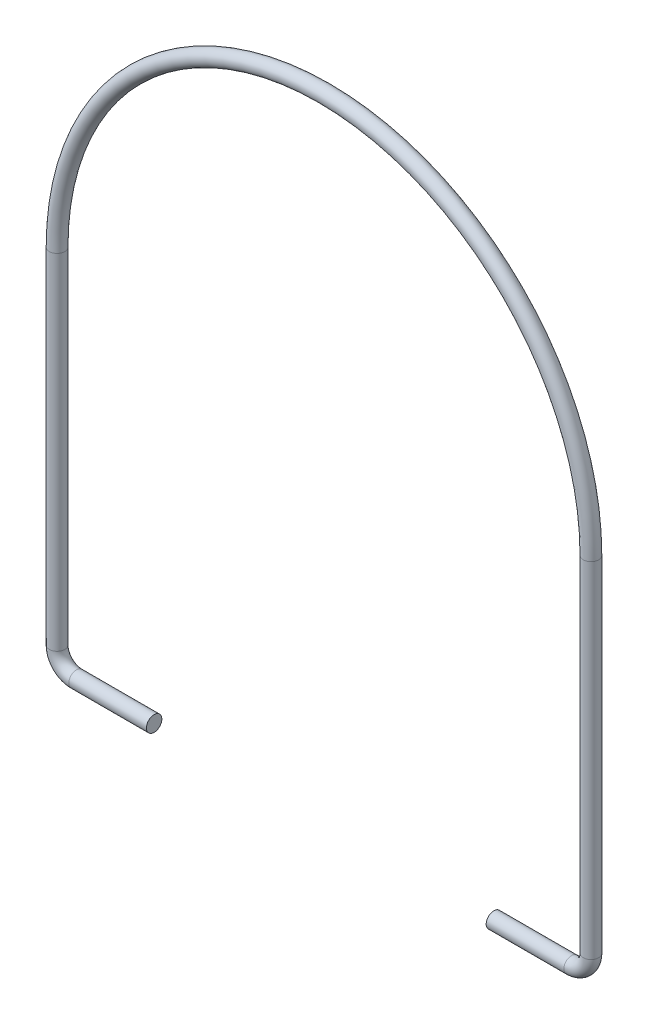
SolidWorks part; units mm, degrees
ref_plane "Front Plane" through (0, 0, 0) normal (0, 0, 1) x (1, 0, 0)
ref_plane "Top Plane" through (0, 0, 0) normal (0, 1, 0) x (1, 0, 0)
ref_plane "Right Plane" through (0, 0, 0) normal (1, 0, 0) x (0, 0, -1)
sketch "Sketch1" plane through (0, 0, 0) normal (0, 0, 1) x (1, 0, 0)
  line L0 (0, 0) -> (-16, 0)
  line L1 (-20, 4) -> (-20, 75)
  line L3 (90, 75) -> (90, 4)
  line L4 (86, 0) -> (70, 0)
  arc A0 (90, 75) -> (-20, 75) centre (35, 75) ccw
  arc A1 (90, 4) -> (86, 0) centre (86, 4) cw
  arc A2 (-20, 4) -> (-16, 0) centre (-16, 4) ccw
  point P10 (90, 0)
  point P13 (-20, 0)
  dimension "D1" = 75
  dimension "D4" = 55
  dimension "D5" = 4
  dimension "D2" = 20
  dimension "D3" = 20
sketch "Sketch2" plane through (0, 0, 0) normal (1, 0, 0) x (0, 0, -1)
  circle A0 centre (0, 0) radius 1.5875
  dimension "D1" = 3.175
sweep "Sweep1" add profiles "Sketch2" path "Sketch1"
